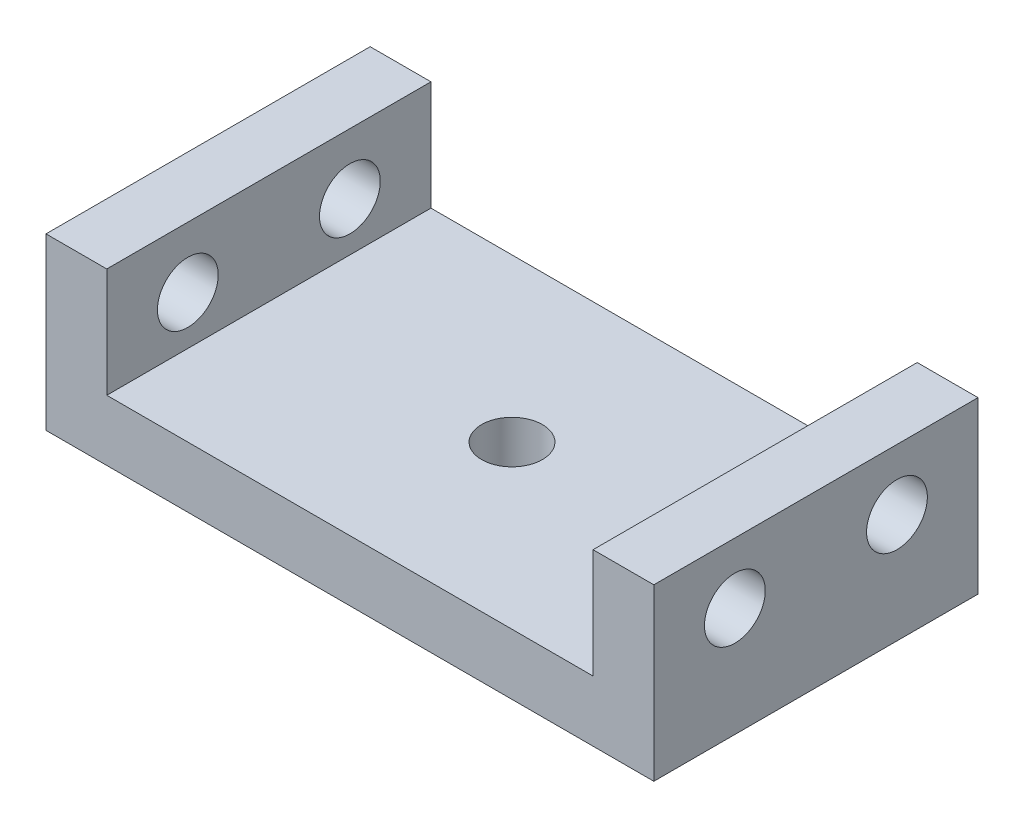
SolidWorks part; units mm, degrees
ref_plane "Front Plane" through (0, 0, 0) normal (0, 0, 1) x (1, 0, 0)
ref_plane "Top Plane" through (0, 0, 0) normal (0, 1, 0) x (1, 0, 0)
ref_plane "Right Plane" through (0, 0, 0) normal (1, 0, 0) x (0, 0, -1)
sketch "Sketch1" plane through (0, 0, 0) normal (0, 1, 0) x (1, 0, 0)
  line L1 (-15, -8) -> (15, -8)
  line L2 (-15, -8) -> (-15, 8)
  line L3 (-15, 8) -> (15, 8)
  line L4 (15, -8) -> (15, 8)
  line L5 (-15, -8) -> (15, 8) construction
  line L6 (-15, 8) -> (15, -8) construction
  point P0 (0, 0)
  dimension "D1" = 16
  dimension "D2" = 30
extrude "Boss-Extrude1" add sketch "Sketch1" along normal blind 3
sketch "Sketch2" plane through (0, 3, 0) normal (0, 1, 0) x (1, 0, 0)
  line L0 (-15, -8) -> (15, -8) construction
  line L1 (-15, 8) -> (-12, 8)
  line L2 (-15, 8) -> (-15, -8)
  line L3 (-15, -8) -> (-12, -8)
  line L4 (-12, 8) -> (-12, -8)
  dimension "D1" = 3
extrude "Boss-Extrude2" add sketch "Sketch2" along normal blind 5.4
sketch "Sketch3" plane through (-15, 0, 0) normal (-1, 0, 0) x (0, 0, 1)
  line L0 (-8, 8.4) -> (-8, 0) construction
  line L1 (8, 8.4) -> (8, 0) construction
  line L2 (-8, 8.4) -> (8, 8.4) construction
  circle A0 centre (-4, 5.4) radius 1.5
  circle A1 centre (4, 5.4) radius 1.5
  dimension "D1" = 3
  dimension "D2" = 3
  dimension "D3" = 4
  dimension "D4" = 4
  dimension "D5" = 3
  dimension "D6" = 3
extrude "Cut-Extrude1" cut sketch "Sketch3" against normal blind 5.4
mirror "Mirror1" about plane through (0, 0, 0) normal (1, 0, 0) of "Cut-Extrude1", "Boss-Extrude2"
sketch "Sketch4" plane through (0, 3, 0) normal (0, 1, 0) x (1, 0, 0)
  circle A0 centre (0, 0) radius 1.5
  dimension "D1" = 3
extrude "Cut-Extrude2" cut sketch "Sketch4" against normal blind 10
equation "\"D2@Sketch3\"=\"D1@Sketch3\""
